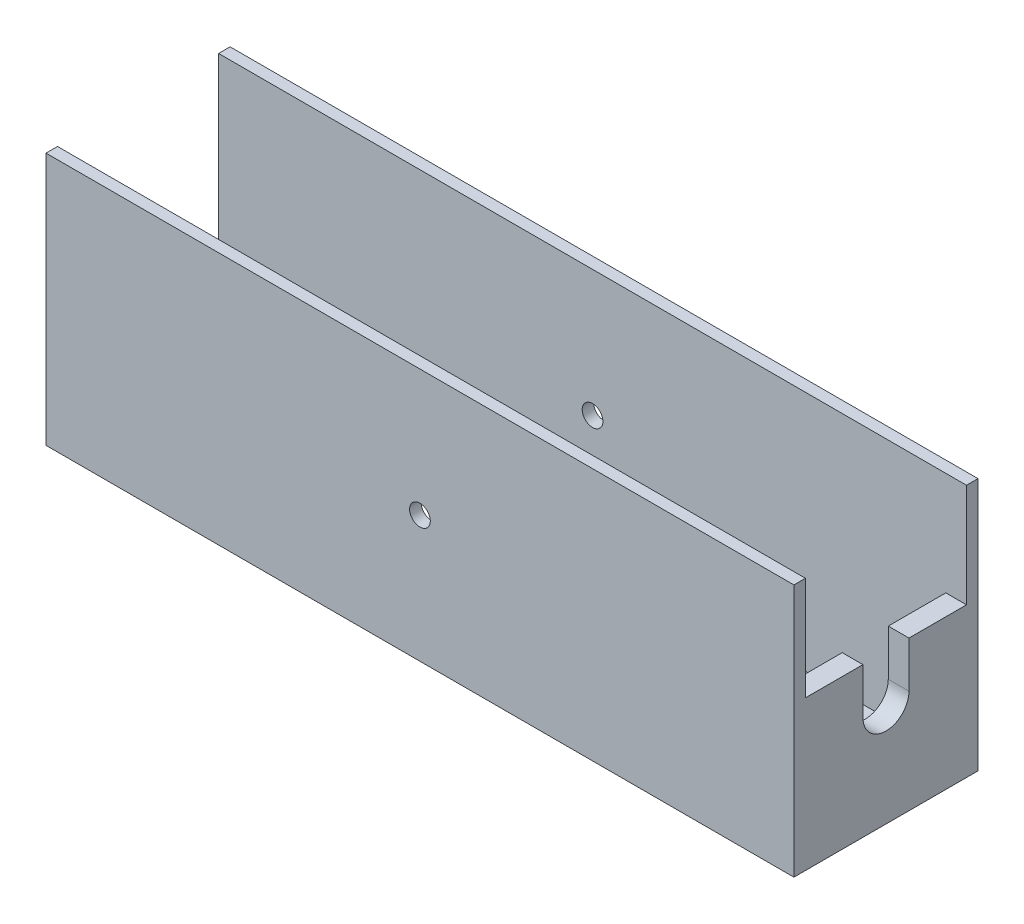
SolidWorks part; units mm, degrees
ref_plane "Front Plane" through (0, 0, 0) normal (0, 0, 1) x (1, 0, 0)
ref_plane "Top Plane" through (0, 0, 0) normal (0, 1, 0) x (1, 0, 0)
ref_plane "Right Plane" through (0, 0, 0) normal (1, 0, 0) x (0, 0, -1)
sketch "Sketch1" plane through (0, 0, 0) normal (0, 1, 0) x (1, 0, 0)
  line L1 (-162.5, 5.5076) -> (162.5, 5.5076)
  line L2 (-162.5, 5.5076) -> (-162.5, 85.5076)
  line L3 (-162.5, 85.5076) -> (162.5, 85.5076)
  line L4 (162.5, 5.5076) -> (162.5, 85.5076)
  point P0 (0, 45.5076)
  dimension "D1" = 325
  dimension "D2" = 80
extrude "Boss-Extrude1" add sketch "Sketch1" against normal blind 5
sketch "Sketch2" plane through (0, 0, 0) normal (0, 1, 0) x (1, 0, 0)
  line L0 (-162.5, 45.5076) -> (162.5, 45.5076) construction
  line L1 (-162.5, 85.5076) -> (-162.5, 5.5076) construction
  line L2 (162.5, 5.5076) -> (162.5, 85.5076) construction
  line L3 (0, 5.5076) -> (0, 85.5076)
  line L4 (-162.5, 5.5076) -> (162.5, 5.5076) construction
  line L5 (162.5, 85.5076) -> (-162.5, 85.5076) construction
  line L6 (-150.6094, 80.5076) -> (-162.5, 80.5076)
  line L7 (-162.5, 85.5076) -> (162.5, 85.5076)
  line L9 (-162.5, 5.5076) -> (162.5, 5.5076)
  line L10 (162.5, 85.5076) -> (162.5, 5.5076)
  line L11 (-150.6094, 10.5076) -> (153.5, 10.5076)
  line L13 (-150.6094, 80.5076) -> (153.5, 80.5076)
  line L14 (153.5, 10.5076) -> (153.5, 80.5076)
  line L17 (-162.5, 80.5076) -> (-162.5, 85.5076)
  line L18 (-150.6094, 10.5076) -> (-162.5, 10.5076)
  line L19 (-162.5, 10.5076) -> (-162.5, 5.5076)
  point P12 (0, 45.5076)
  point P18 (0, 45.5076)
  dimension "D1" = 9
  dimension "D2" = 5
  dimension "D3" = 5
extrude "Boss-Extrude2" add sketch "Sketch2" along normal blind 105 contours L13 L14 L11 L18 L19 L9 L10 L7 L17 L6
sketch "Sketch3" plane through (0, 0, -5.5076) normal (0, 0, 1) x (1, 0, 0)
  line L0 (-162.5, 50) -> (162.5, 50) construction
  line L1 (-162.5, -5) -> (-162.5, 105) construction
  line L2 (162.5, -5) -> (162.5, 105) construction
  line L4 (-162.5, -5) -> (162.5, -5) construction
  line L5 (0, 105) -> (0, -5) construction
  line L6 (-162.5, 105) -> (162.5, 105) construction
  circle A0 centre (0, 50) radius 4.5
  dimension "D1" = 9
extrude "Cut-Extrude1" cut sketch "Sketch3" against normal through all both and the other way through all
sketch "Sketch4" plane through (0, 0, 0) normal (0, 1, 0) x (1, 0, 0)
  line L0 (-162.5, 45.5076) -> (-67.5, 45.5076) construction
  line L1 (-162.5, 80.5076) -> (-162.5, 10.5076) construction
  line L2 (153.5, 10.5076) -> (153.5, 80.5076) construction
  line L6 (153.5, 80.5076) -> (-162.5, 80.5076) construction
  line L7 (-67.5, 10.5076) -> (52.5, 10.5076)
  line L8 (-67.5, 10.5076) -> (-67.5, 80.5076)
  line L9 (-67.5, 80.5076) -> (52.5, 80.5076)
  line L10 (52.5, 10.5076) -> (52.5, 80.5076)
  line L13 (52.5, 45.5076) -> (153.5, 45.5076) construction
  point P12 (-4.5, 45.5076)
  dimension "D1" = 120
  dimension "D2" = 95
extrude "Cut-Extrude2" cut sketch "Sketch4" against normal blind 105 contours L8 L7 L10 L9
sketch "Sketch5" plane through (162.5, 0, 0) normal (1, 0, 0) x (0, 0, -1)
  line L0 (10.5076, 109.6308) -> (10.5076, 105) construction
  line L1 (85.5076, 105) -> (5.5076, 105) construction
  line L2 (85.5076, -5) -> (85.5076, 105) construction
  line L3 (10.5076, 105) -> (80.5076, 105)
  line L4 (10.5076, 105) -> (10.5076, 60)
  line L5 (10.5076, 60) -> (80.5076, 60)
  line L6 (80.5076, 105) -> (80.5076, 60)
  line L7 (5.5076, -5) -> (5.5076, 105) construction
  line L8 (5.5076, -5) -> (85.5076, -5) construction
  line L10 (35.5076, 60) -> (55.5076, 60)
  line L11 (35.5076, 60) -> (35.5076, 40)
  line L12 (35.5076, 40) -> (55.5076, 40)
  line L13 (55.5076, 60) -> (55.5076, 40)
  arc A0 (35.5076, 40) -> (55.5076, 40) centre (45.5076, 40) ccw
  point P13 (45.5076, 60)
  dimension "D1" = 5
  dimension "D2" = 5
  dimension "D3" = 65
  dimension "D4" = 20
  dimension "D5" = 20
  dimension "D6" = 0
extrude "Cut-Extrude3" cut sketch "Sketch5" against normal blind 105 contours L12 A0 | L13 L5 L11 L12 | L6 L7 L4 L5
